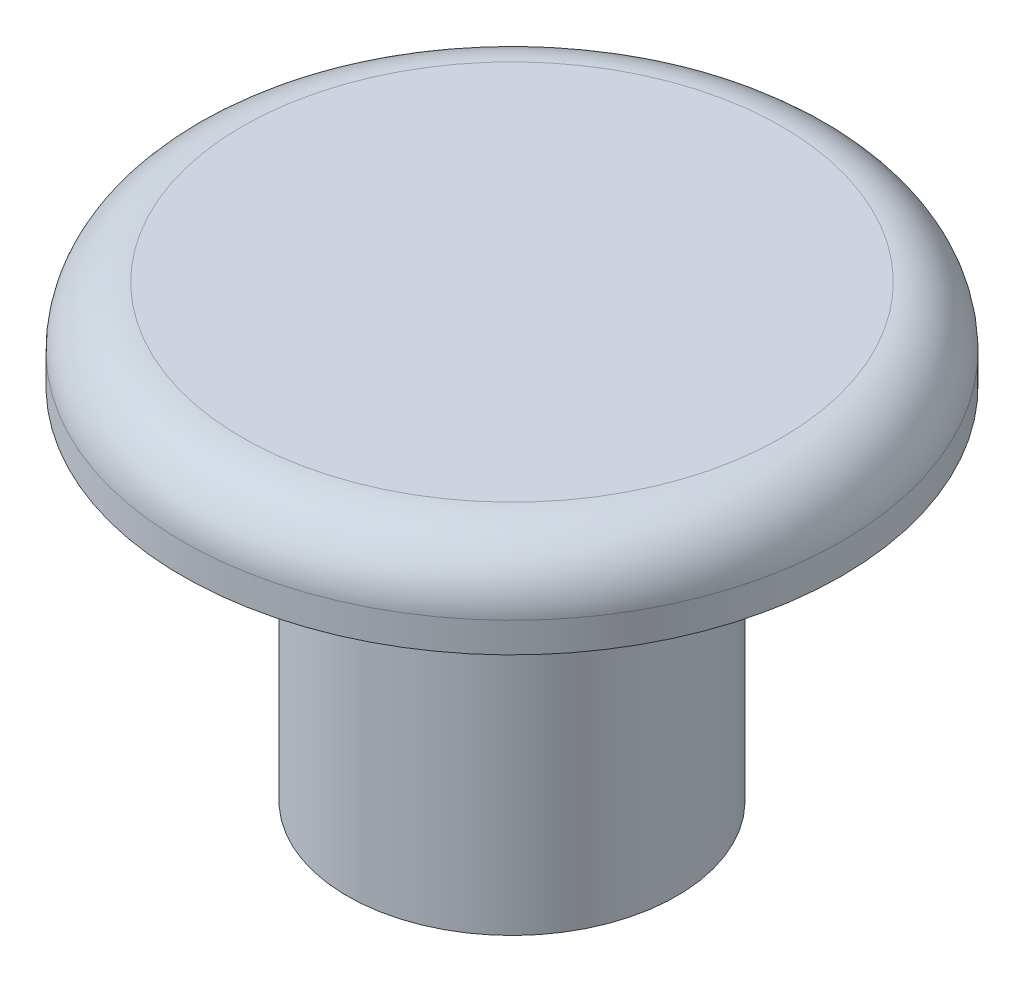
SolidWorks part; units mm, degrees
ref_plane "Front Plane" through (0, 0, 0) normal (0, 0, 1) x (1, 0, 0)
ref_plane "Top Plane" through (0, 0, 0) normal (0, 1, 0) x (1, 0, 0)
ref_plane "Right Plane" through (0, 0, 0) normal (1, 0, 0) x (0, 0, -1)
sketch "Sketch1" plane through (0, 0, 0) normal (0, 0, 1) x (1, 0, 0)
  line L0 (0, 0) -> (5.5, 0)
  line L1 (5.5, 0) -> (5.5, 12)
  line L2 (5.5, 12) -> (11, 12)
  line L3 (11, 12) -> (11, 15)
  line L4 (11, 15) -> (0, 15)
  line L5 (0, 15) -> (0, 0)
  dimension "D1" = 5.5
  dimension "D2" = 12
  dimension "D3" = 3
  dimension "D4" = 11
revolve "Revolve1" add sketch "Sketch1" angle 360 about L5
fillet "Fillet2" radius 2 1 edges at (-11, 15, 0)
